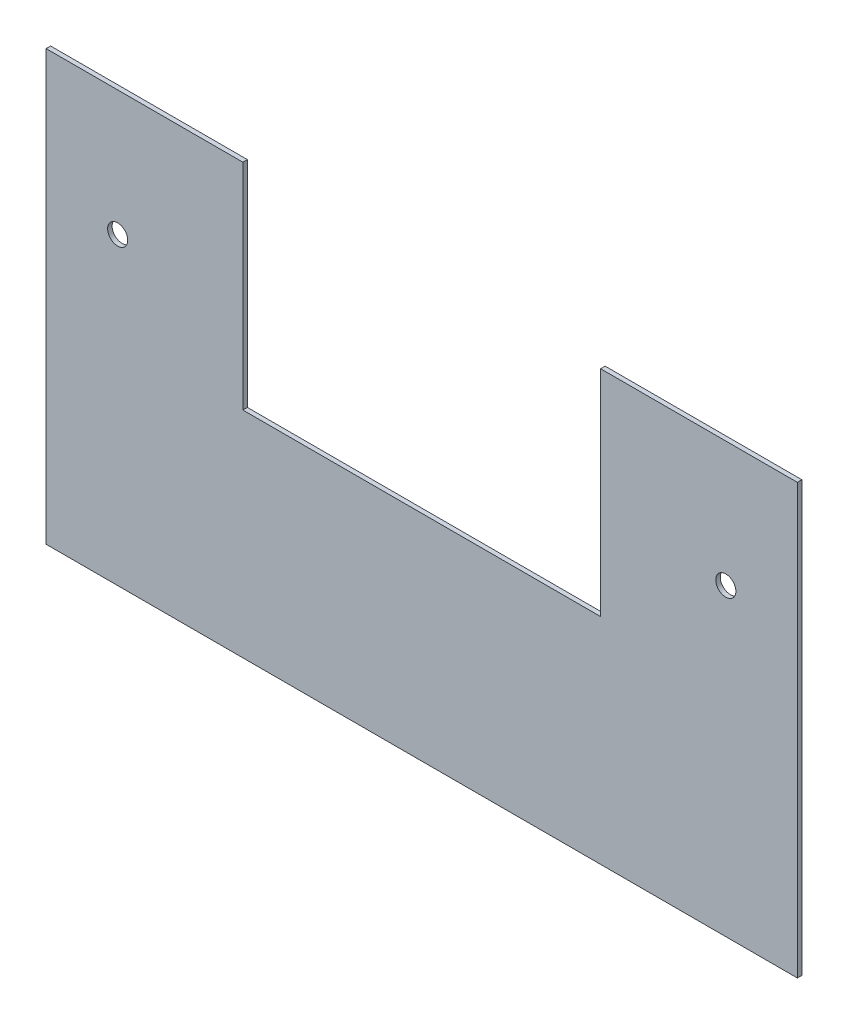
SolidWorks part; units mm, degrees
ref_plane "Front Plane" through (0, 0, 0) normal (0, 0, 1) x (1, 0, 0)
ref_plane "Top Plane" through (0, 0, 0) normal (0, 1, 0) x (1, 0, 0)
ref_plane "Right Plane" through (0, 0, 0) normal (1, 0, 0) x (0, 0, -1)
sketch "Sketch1" plane through (0, 0, 0) normal (0, 0, 1) x (1, 0, 0)
  line L0 (63.5, 76.2) -> (133.35, 76.2)
  line L1 (-133.35, 76.2) -> (-63.5, 76.2)
  line L2 (-133.35, 76.2) -> (-133.35, -76.2)
  line L3 (-133.35, -76.2) -> (133.35, -76.2)
  line L4 (133.35, 76.2) -> (133.35, -76.2)
  line L5 (-133.35, 76.2) -> (133.35, -76.2) construction
  line L6 (-133.35, -76.2) -> (133.35, 76.2) construction
  line L8 (-63.5, 76.2) -> (-63.5, 0)
  line L9 (-63.5, 0) -> (63.5, 0)
  line L10 (63.5, 76.2) -> (63.5, 0)
  point P0 (0, 0)
  dimension "D1" = 152.4
  dimension "D2" = 266.7
  dimension "D3" = 127
  dimension "D4" = 69.85
  dimension "D5" = 76.2
extrude "Boss-Extrude1" add sketch "Sketch1" along normal blind 1.6002
hole_wizard "1/4 Clearance Hole1" positions "Sketch3" profile "Sketch2" hole size "1/4" standard "ANSI Inch" end condition through all
sketch "Sketch3" plane through (0, 0, 1.6002) normal (0, 0, 1) x (1, 0, 0)
  line L0 (133.35, 76.2) -> (63.5, 76.2) construction
  line L2 (63.5, 76.2) -> (63.5, 0) construction
  line L3 (-63.5, 0) -> (-63.5, 76.2) construction
  point P0 (-107.95, 31.75)
  point P2 (107.95, 31.75)
  dimension "D1" = 44.45
  dimension "D2" = 44.45
  dimension "D3" = 44.45
sketch "Sketch2" plane through (-107.95, 31.75, 1.6002) normal (1, 0, 0) x (0, -1, 0)
  line L0 (0, 0) -> (0, 1.6002)
  line L1 (0, 1.6002) -> (3.5712, 1.6002)
  line L2 (3.5712, 1.6002) -> (3.5712, 0)
  line L5 (3.5712, 0) -> (0, 0)
  line L11 (0, -6.35) -> (0, 107.95) construction
  dimension "Thru Hole Dia." = 7.1425
  dimension "Thru Hole Depth" = 1.6002
